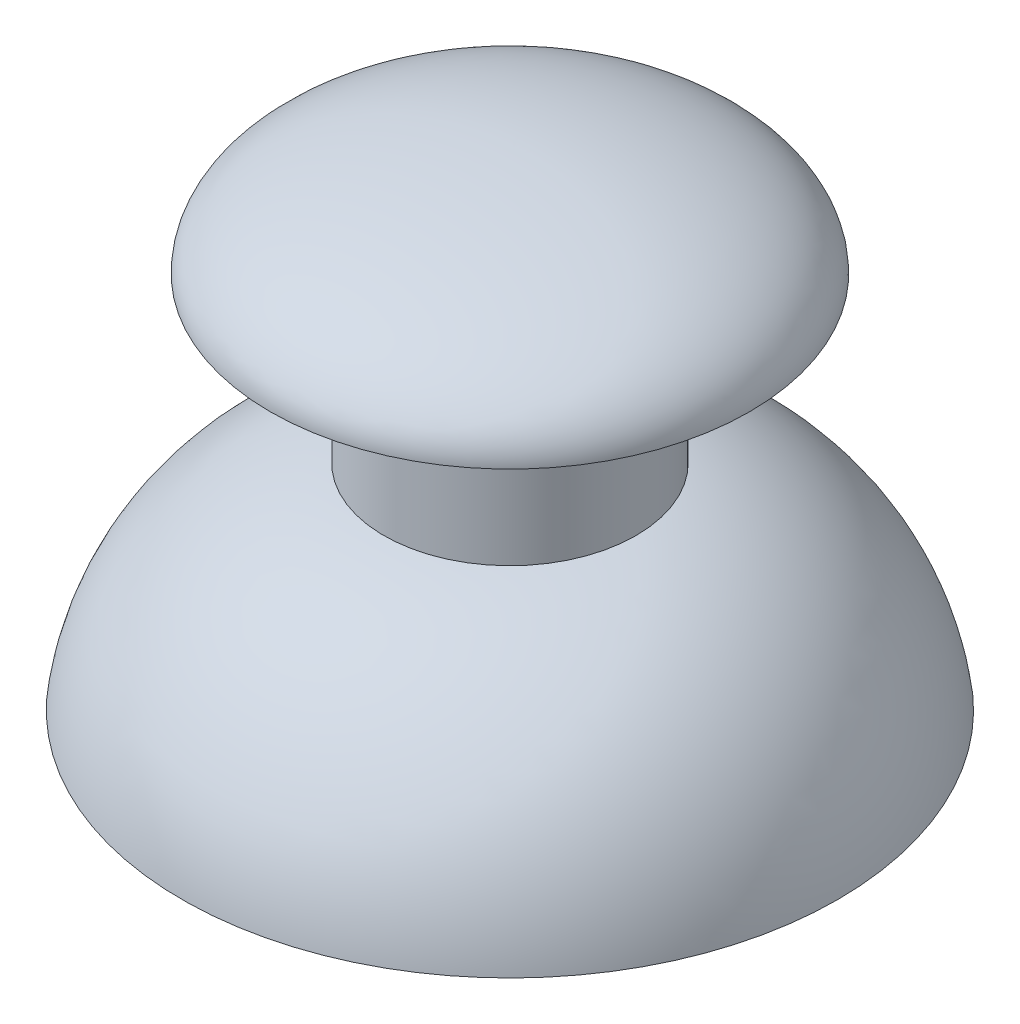
SolidWorks part; units mm, degrees
ref_plane "Plan de face" through (0, 0, 0) normal (0, 0, 1) x (1, 0, 0)
ref_plane "Plan de dessus" through (0, 0, 0) normal (0, 1, 0) x (1, 0, 0)
ref_plane "Plan de droite" through (0, 0, 0) normal (1, 0, 0) x (0, 0, -1)
sketch "Esquisse1" plane through (0, 0, 0) normal (0, 0, 1) x (1, 0, 0)
  line L0 (0, 0) -> (0, 19) construction
  line L1 (0, 19) -> (0, 0) construction
  line L2 (9.5, 15) -> (5, 14)
  line L3 (5, 14) -> (5, 8.5)
  line L4 (0, 8.5) -> (1, 8.5)
  line L5 (1, 8.5) -> (1, 3)
  line L6 (1, 3) -> (3, 3)
  line L7 (3, 3) -> (3, 14)
  line L8 (3, 14) -> (4, 14)
  line L9 (4, 14) -> (4, 7.6383)
  line L10 (11.9855, 0.032) -> (13, 0)
  line L11 (0, 8.5) -> (0, 19)
  arc A0 (13, 0) -> (5, 8.5) centre (3.0869, -1.3153) ccw
  arc A1 (4, 7.6383) -> (11.9855, 0.032) centre (3.0869, -1.3153) cw
  ellipse E0 centre (0, 15) end of major axis (-9.5, 15) minor radius 4 (9.5, 15) -> (0, 19) ccw
  dimension "D7" = 10
  dimension "D15" = 1
  dimension "D1" = 19
  dimension "D2" = 4
  dimension "D3" = 10
  dimension "D4" = 1
  dimension "D5" = 5.5
  dimension "D6" = 26
  dimension "D8" = 19
  dimension "D9" = 8.5
  dimension "D10" = 14
  dimension "D11" = 3
  dimension "D12" = 6
  dimension "D13" = 8
  dimension "D14" = 2
revolve "Révolution1" add sketch "Esquisse1" angle 360 about L0
chamfer "Chanfrein1" [suppressed] distance 0.8 angle 60
